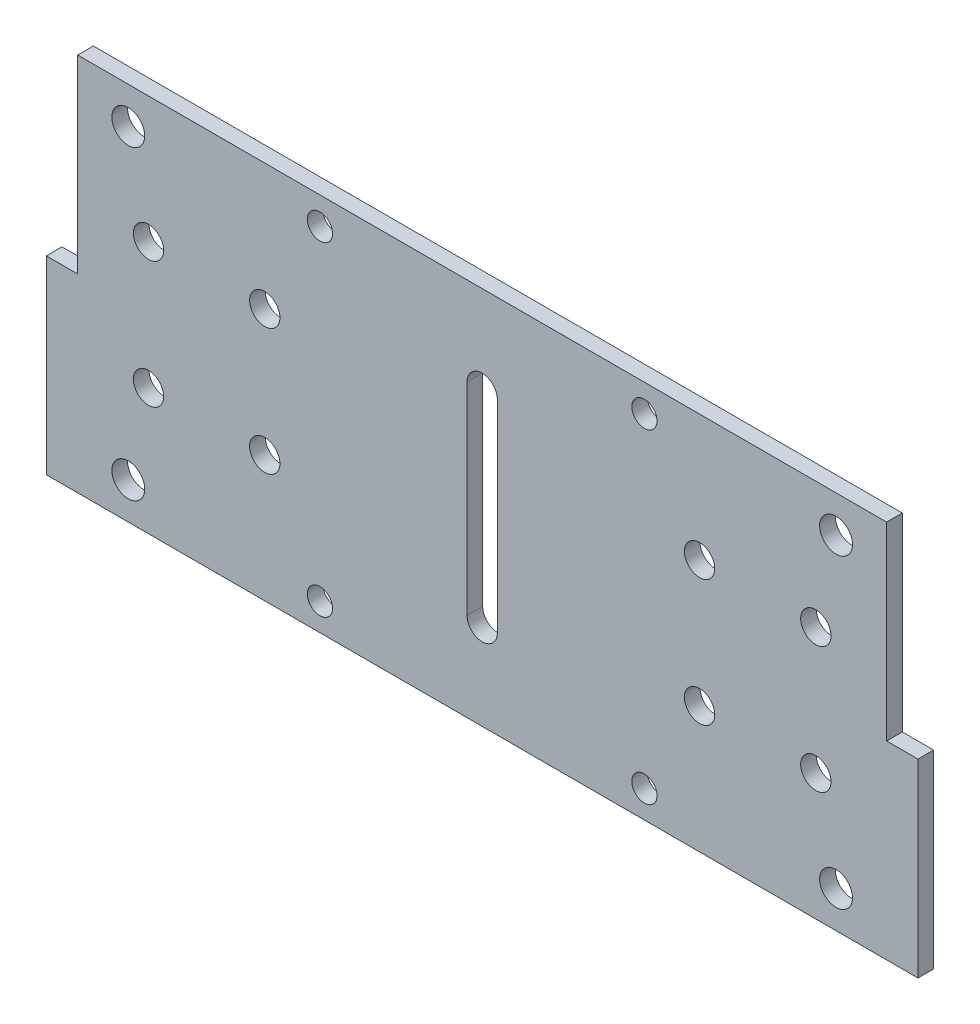
SolidWorks part; units mm, degrees
material "Teak"
ref_plane "Front Plane" through (0, 0, 0) normal (0, 0, 1) x (1, 0, 0)
ref_plane "Top Plane" through (0, 0, 0) normal (0, 1, 0) x (1, 0, 0)
ref_plane "Right Plane" through (0, 0, 0) normal (1, 0, 0) x (0, 0, -1)
sketch "Sketch1" plane through (0, 0, 0) normal (0, 0, 1) x (1, 0, 0)
  line L1 (-80, -37.5) -> (80, -37.5)
  line L2 (-80, -37.5) -> (-80, 37.5)
  line L3 (-80, 37.5) -> (80, 37.5)
  line L4 (80, -37.5) -> (80, 37.5)
  line L5 (-80, -37.5) -> (80, 37.5) construction
  line L6 (-80, 37.5) -> (80, -37.5) construction
  point P0 (0, 0)
  dimension "D1" = 160
  dimension "D2" = 75
extrude "Boss-Extrude1" add sketch "Sketch1" along normal blind 3.1
sketch "Sketch2" plane through (0, 0, 3.1) normal (0, 0, 1) x (1, 0, 0)
  line L0 (80, 0) -> (80, -37.5)
  line L1 (80, 0) -> (86.2, 0)
  line L2 (80, -37.5) -> (86.2, -37.5)
  line L3 (86.2, 0) -> (86.2, -37.5)
  line L4 (80, -37.5) -> (80, 37.5) construction
  line L5 (0, 0) -> (0, 37.5) construction
  line L6 (80, 37.5) -> (-80, 37.5) construction
  line L7 (-86.2, 0) -> (-86.2, -37.5)
  line L8 (-80, -37.5) -> (-86.2, -37.5)
  line L9 (-80, 0) -> (-86.2, 0)
  line L10 (-80, 0) -> (-80, -37.5)
  dimension "D1" = 6.2
extrude "Boss-Extrude2" add sketch "Sketch2" against normal through all
sketch "Sketch3" plane through (0, 0, 3.1) normal (0, 0, 1) x (1, 0, 0)
  line L0 (0, 0) -> (0.4594, 0) construction
  line L1 (-38.1, -38.1) -> (38.1, -38.1) construction
  line L2 (-38.1, -38.1) -> (-38.1, 38.1) construction
  line L3 (-38.1, 38.1) -> (38.1, 38.1) construction
  line L4 (38.1, -38.1) -> (38.1, 38.1) construction
  line L5 (-38.1, -38.1) -> (38.1, 38.1) construction
  line L6 (-38.1, 38.1) -> (38.1, -38.1) construction
  line L7 (0, 36.4611) -> (0, 0) construction
  line L8 (0, 0) -> (3, 0) construction
  line L9 (3, -20) -> (3, 20)
  line L10 (3, 20) -> (0, 20) construction
  line L11 (-3, -20) -> (-3, 20)
  line L12 (-80, 37.5) -> (-80, 0) construction
  line L13 (80, 37.5) -> (-80, 37.5) construction
  line L14 (-66, 12.5) -> (-43, 12.5) construction
  line L15 (-43, 12.5) -> (-43, 22.28) construction
  line L16 (0, 0) -> (-66, 0) construction
  circle A0 centre (32.0896, 32.0896) radius 2.5
  circle A1 centre (32.0896, -32.0896) radius 2.5
  circle A2 centre (-32.0896, -32.0896) radius 2.5
  circle A3 centre (-32.0896, 32.0896) radius 2.5
  arc A4 (3, 20) -> (-3, 20) centre (0, 20) ccw
  arc A5 (3, -20) -> (-3, -20) centre (0, -20) cw
  circle A6 centre (-66, 12.5) radius 3
  circle A7 centre (-43, 12.5) radius 3
  circle A8 centre (-43, -12.5) radius 3
  circle A9 centre (-66, -12.5) radius 3
  circle A10 centre (43, 12.5) radius 3
  circle A11 centre (66, 12.5) radius 3
  circle A12 centre (66, -12.5) radius 3
  circle A13 centre (43, -12.5) radius 3
  circle A14 centre (-70, -30.2588) radius 3.25
  circle A15 centre (70, -30.2588) radius 3.25
  circle A16 centre (-70, 30.2588) radius 3.25
  circle A17 centre (70, 30.2588) radius 3.25
  point P0 (0, 0)
  point P17 (0, 0)
  point P26 (-3, 0)
  dimension "D3" = 5
  dimension "D8" = 6
  dimension "D9" = 14
  dimension "D13" = 6.5
  dimension "D1" = 76.2
  dimension "D2" = 76.2
  dimension "D4" = 8.5
  dimension "D6" = 6
  dimension "D7" = 40
  dimension "D10" = 2
  dimension "D11" = 25
  dimension "D12" = 9.78
  dimension "D14" = 10
  dimension "D5" = 4
extrude "Cut-Extrude1" cut sketch "Sketch3" against normal through all
equation "\"thick\" = 3.1mm"
equation "\"small_bearing_outer\"=12.9mm"
equation "\"servo1_L\"=40.7mm"
equation "\"servo1_W\"=20.5mm"
equation "\"servo1_H\"=43.5mm"
equation "\"servo1_hL\"=49mm"
equation "\"servo1_hW\"=10mm"
equation "\"servo1_H2\"=27mm"
equation "\"large_bearing_inner\"=2.75in"
equation "\"large_bearing_outer\"=4.75in"
equation "\"large_bearing_thick\"=3/8in"
equation "\"large_bearing_h1\"=3.25in"
equation "\"large_bearing_h2\"=4.25in"
equation "\"D1@Boss-Extrude1\"=\"thick\""
equation "\"D1@Sketch2\"=2*\"thick\""
equation "\"D2@Sketch3\"=3in"
